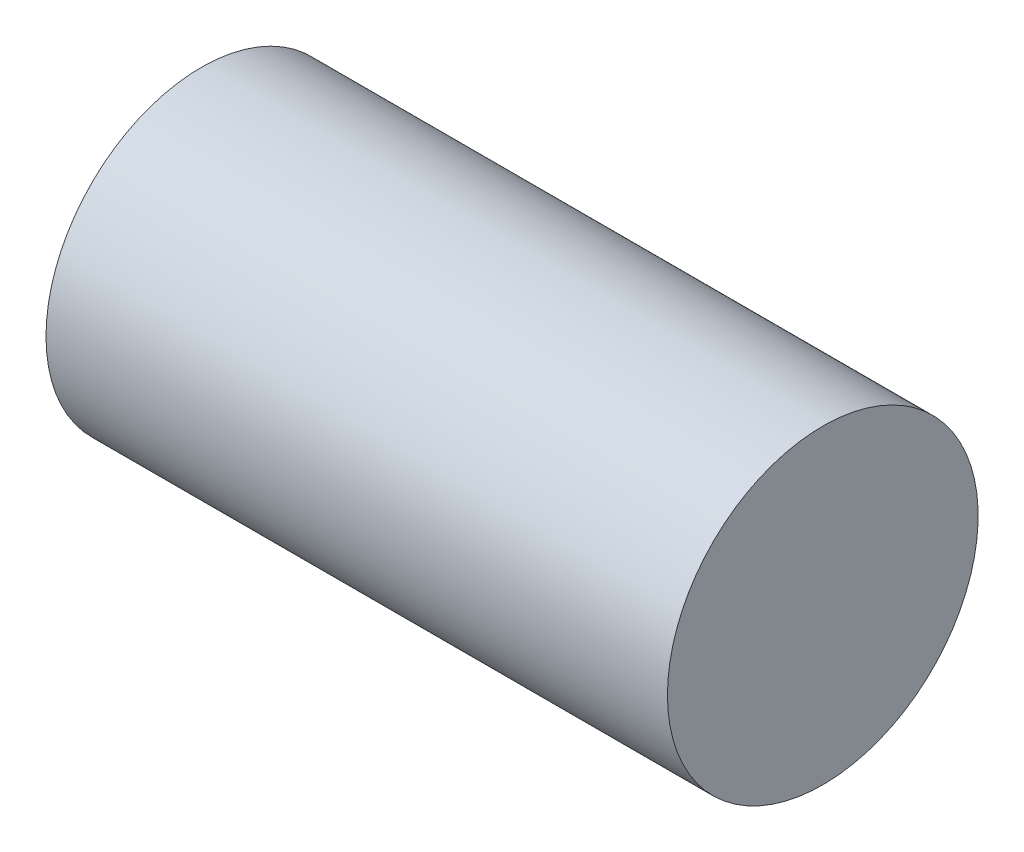
SolidWorks part; units mm, degrees
ref_plane "Front Plane" through (0, 0, 0) normal (0, 0, 1) x (1, 0, 0)
ref_plane "Top Plane" through (0, 0, 0) normal (0, 1, 0) x (1, 0, 0)
ref_plane "Right Plane" through (0, 0, 0) normal (1, 0, 0) x (0, 0, -1)
sketch "Sketch1" plane through (0, 0, 0) normal (0, 0, 1) x (1, 0, 0)
  line L0 (0, 6.35) -> (21.59, 6.35)
  line L1 (21.59, 6.35) -> (21.59, 0)
  line L2 (21.59, 0) -> (76.2, 0)
  line L3 (76.2, 0) -> (76.2, 19.05)
  line L4 (76.2, 19.05) -> (0, 19.05)
  line L5 (0, 19.05) -> (0, 6.35)
  point P2 (0, 0)
  dimension "D1" = 6.35
  dimension "D2" = 12.7
  dimension "D3" = 76.2
  dimension "D4" = 21.59
revolve "Revolve1" add sketch "Sketch1" angle 360 about L2
